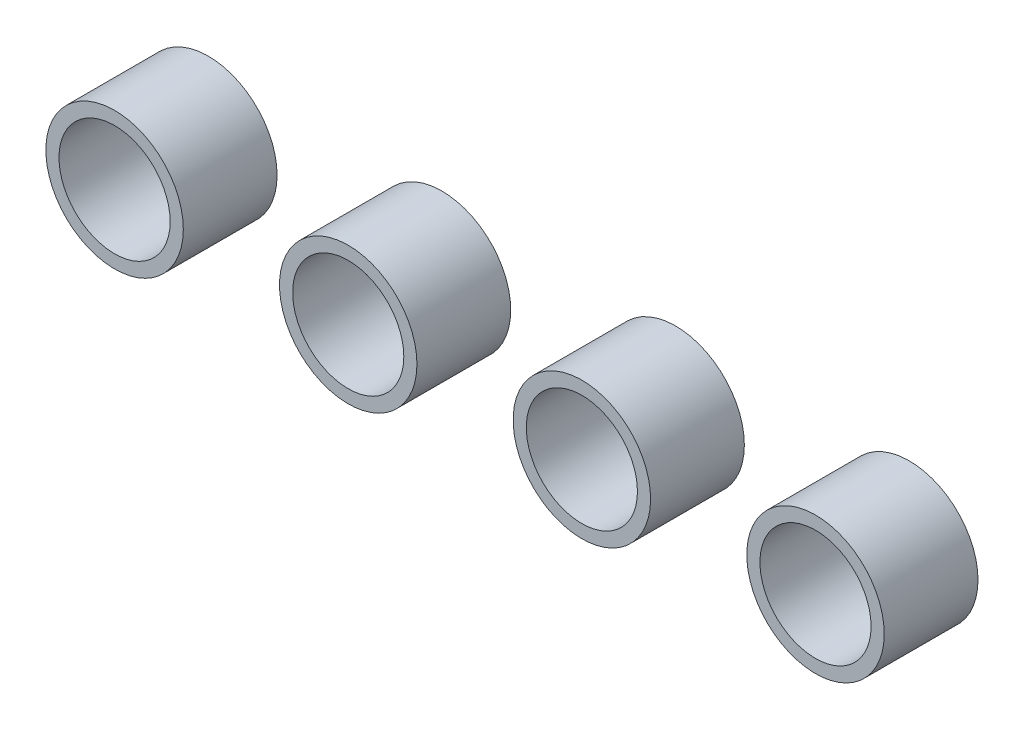
SolidWorks part; units mm, degrees
ref_plane "Front Plane" through (0, 0, 0) normal (0, 0, 1) x (1, 0, 0)
ref_plane "Top Plane" through (0, 0, 0) normal (0, 1, 0) x (1, 0, 0)
ref_plane "Right Plane" through (0, 0, 0) normal (1, 0, 0) x (0, 0, -1)
sketch "Sketch1" plane through (0, 0, 0) normal (0, 0, 1) x (1, 0, 0)
  line L0 (21.59, 0) -> (51.816, 0) construction
  line L1 (94.996, 0) -> (125.222, 0) construction
  line L2 (168.402, 0) -> (198.628, 0) construction
  line L10 (0, 17.4625) -> (0, -17.4625) construction
  line L11 (73.406, 17.4625) -> (73.406, -17.4625) construction
  line L12 (146.812, 17.4625) -> (146.812, -17.4625) construction
  line L13 (220.218, 17.4625) -> (220.218, -17.4625) construction
  line L14 (0, 16.2179) -> (0, 17.4625) construction
  circle A0 centre (0, 0) radius 17.4625
  circle A1 centre (73.406, 0) radius 17.4625
  circle A2 centre (146.812, 0) radius 17.4625
  circle A3 centre (220.218, 0) radius 17.4625
  circle A8 centre (0, 0) radius 21.59
  circle A9 centre (73.406, 0) radius 21.59
  circle A10 centre (146.812, 0) radius 21.59
  circle A11 centre (220.218, 0) radius 21.59
  dimension "D4" = 34.925
  dimension "D7" = 34.925
  dimension "D10" = 34.925
  dimension "D12" = 30.226
  dimension "D2" = 43.18
  dimension "D3" = 43.18
  dimension "D5" = 43.18
  dimension "D6" = 43.18
  dimension "D8" = 30.226
  dimension "D9" = 30.226
extrude "Boss-Extrude4" add sketch "Sketch1" along normal blind 29.464
